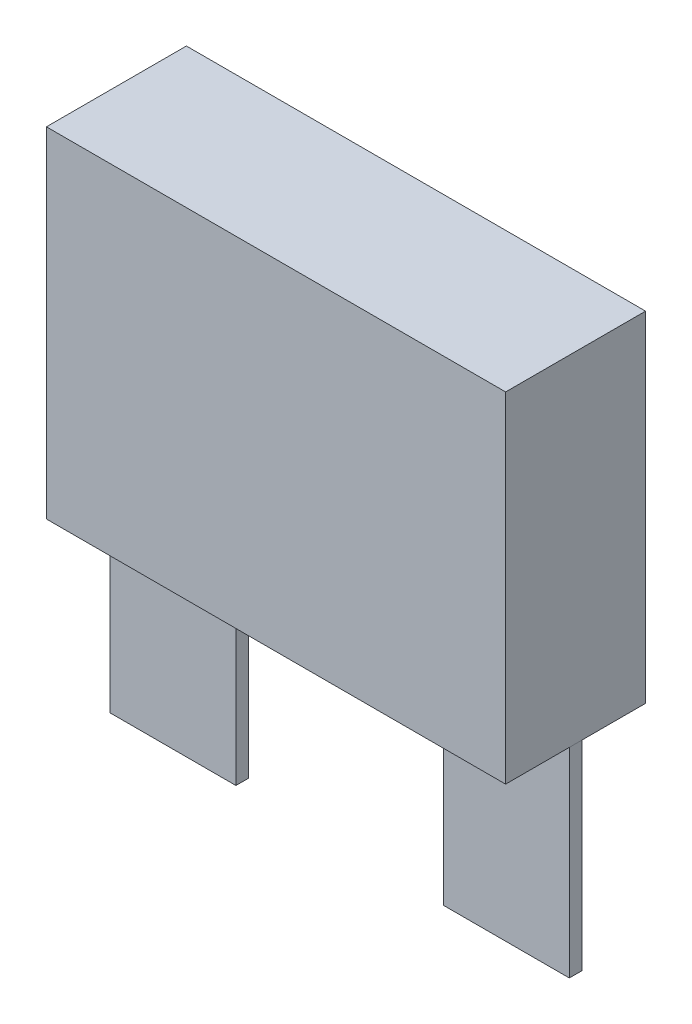
SolidWorks part; units mm, degrees
ref_plane "Front Plane" through (0, 0, 0) normal (0, 0, 1) x (1, 0, 0)
ref_plane "Top Plane" through (0, 0, 0) normal (0, 1, 0) x (1, 0, 0)
ref_plane "Right Plane" through (0, 0, 0) normal (1, 0, 0) x (0, 0, -1)
sketch "Sketch1" plane through (0, 0, 0) normal (0, 1, 0) x (1, 0, 0)
  line L1 (-14.6, -4.45) -> (14.6, -4.45)
  line L2 (-14.6, -4.45) -> (-14.6, 4.45)
  line L3 (-14.6, 4.45) -> (14.6, 4.45)
  line L4 (14.6, -4.45) -> (14.6, 4.45)
  line L5 (-14.6, -4.45) -> (14.6, 4.45) construction
  line L6 (-14.6, 4.45) -> (14.6, -4.45) construction
  point P0 (0, 0)
  dimension "D1" = 8.9
  dimension "D2" = 29.2
extrude "Boss-Extrude1" add sketch "Sketch1" along normal blind 21.6
sketch "Sketch2" plane through (0, 0, 0) normal (0, -1, 0) x (1, 0, 0)
  line L0 (-14.6, -4.45) -> (-14.6, 4.45) construction
  line L1 (-14.6, -0.4) -> (-6.6, -0.4)
  line L2 (-14.6, -0.4) -> (-14.6, 0.4)
  line L3 (-14.6, 0.4) -> (-6.6, 0.4)
  line L4 (-6.6, -0.4) -> (-6.6, 0.4)
  line L5 (14.6, 4.45) -> (14.6, -4.45) construction
  line L6 (14.6, -0.4) -> (6.6, -0.4)
  line L7 (14.6, -0.4) -> (14.6, 0.4)
  line L8 (14.6, 0.4) -> (6.6, 0.4)
  line L9 (6.6, -0.4) -> (6.6, 0.4)
  point P12 (6.6, 0)
  point P13 (-6.6, 0)
  dimension "D1" = 0.8
  dimension "D2" = 8
extrude "Boss-Extrude2" add sketch "Sketch2" along normal blind 12.7 separate body
